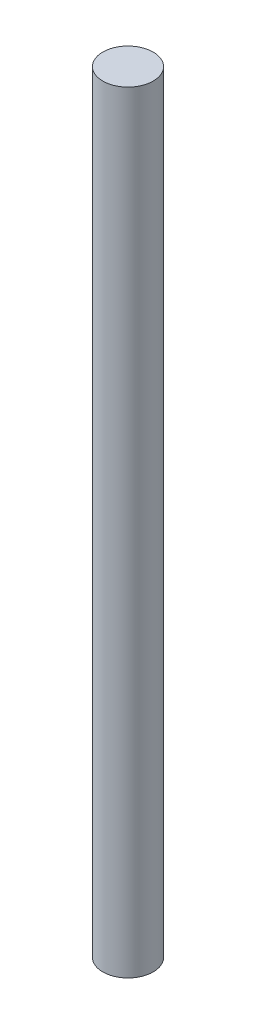
SolidWorks part; units mm, degrees
ref_plane "Top Plane" through (0, 0, 0) normal (0, 0, 1) x (1, 0, 0)
ref_plane "Front Plane" through (0, 0, 0) normal (0, 1, 0) x (1, 0, 0)
ref_plane "Right Plane" through (0, 0, 0) normal (1, 0, 0) x (0, 0, -1)
sketch "Profile Sketch" plane through (0, 0, 0) normal (0, 1, 0) x (1, 0, 0)
  circle A0 centre (0, 0) radius 4
  dimension "D1" = 8
extrude "Boss-Extrude1" add sketch "Profile Sketch" along normal blind 122.5858
